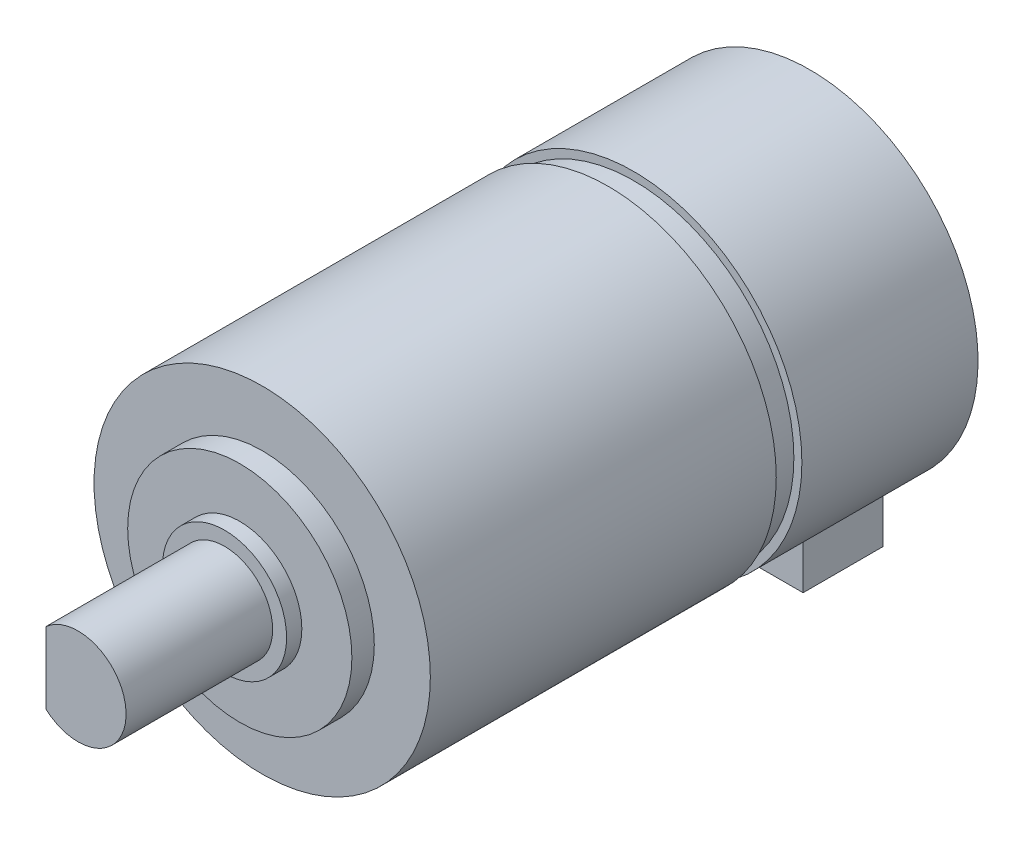
SolidWorks part; units mm, degrees
ref_plane "Plan de face" through (0, 0, 0) normal (0, 0, 1) x (1, 0, 0)
ref_plane "Plan de dessus" through (0, 0, 0) normal (0, 1, 0) x (1, 0, 0)
ref_plane "Plan de droite" through (0, 0, 0) normal (1, 0, 0) x (0, 0, -1)
sketch "Esquisse1" plane through (0, 0, 0) normal (0, 0, 1) x (1, 0, 0)
  circle A0 centre (0, 0) radius 21
  dimension "D1" = 42
extrude "Boss.-Extru.1" add sketch "Esquisse1" along normal blind 22
sketch "Esquisse2" plane through (0, 0, 0) normal (0, 0, -1) x (-1, 0, 0)
  line L1 (-9.15, 26) -> (9.15, 26)
  line L2 (-9.15, 26) -> (-9.15, -26)
  line L3 (-9.15, -26) -> (9.15, -26)
  line L4 (9.15, 26) -> (9.15, -26)
  line L5 (-9.15, 26) -> (9.15, -26) construction
  line L6 (-9.15, -26) -> (9.15, 26) construction
  circle A0 centre (0, 0) radius 21 construction
  circle A1 centre (0, 0) radius 21
  circle M3 centre (0, 0) radius 21
  dimension "D1" = 52
  dimension "D2" = 18.3
extrude "Boss.-Extru.2" add sketch "Esquisse2" against normal blind 10 contours L4 L2 L3 M3
sketch "Esquisse3" plane through (0, 0, 22) normal (0, 0, 1) x (1, 0, 0)
  circle A0 centre (0, 0) radius 20
  dimension "D1" = 40
extrude "Boss.-Extru.3" add sketch "Esquisse3" along normal blind 3.2
sketch "Esquisse4" plane through (0, 0, 25.2) normal (0, 0, 1) x (1, 0, 0)
  circle A0 centre (0, 0) radius 21
  dimension "D1" = 42
extrude "Boss.-Extru.4" add sketch "Esquisse4" along normal blind 43.2
sketch "Esquisse5" plane through (0, 0, 68.4) normal (0, 0, 1) x (1, 0, 0)
  circle A0 centre (0, 0) radius 14
  dimension "D1" = 28
extrude "Boss.-Extru.5" add sketch "Esquisse5" along normal blind 2.8
sketch "Esquisse6" plane through (0, 0, 71.2) normal (0, 0, 1) x (1, 0, 0)
  circle A0 centre (0, 0) radius 7.75
  dimension "D1" = 15.5
extrude "Boss.-Extru.6" add sketch "Esquisse6" along normal blind 1.9
sketch "Esquisse7" plane through (0, 0, 73.1) normal (0, 0, 1) x (1, 0, 0)
  circle A0 centre (0, 0) radius 6
  dimension "D1" = 12
extrude "Boss.-Extru.7" add sketch "Esquisse7" along normal blind 7.8
sketch "Esquisse8" plane through (0, 0, 80.9) normal (0, 0, 1) x (1, 0, 0)
  line L0 (-4, 15.5576) -> (-4, -10.0291)
  line L1 (9.15, -18.9018) -> (9.15, -26) construction
  line L2 (9.15, -18.9018) -> (9.15, -26)
  circle A0 centre (0, 0) radius 6 construction
  circle A1 centre (0, 0) radius 6
  circle M1 centre (0, 0) radius 6
  dimension "D1" = 4
extrude "Boss.-Extru.8" add sketch "Esquisse8" along normal blind 10.5 contours L0 M1
